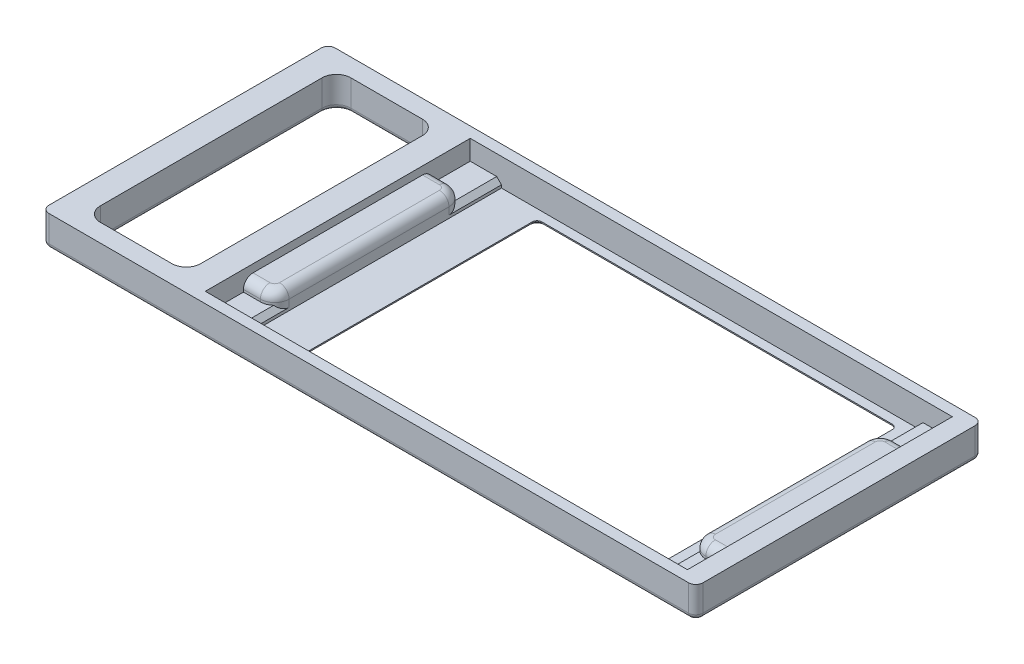
SolidWorks part; units mm, degrees
ref_plane "Front Plane" through (0, 0, 0) normal (0, 0, 1) x (1, 0, 0)
ref_plane "Top Plane" through (0, 0, 0) normal (0, 1, 0) x (1, 0, 0)
ref_plane "Right Plane" through (0, 0, 0) normal (1, 0, 0) x (0, 0, -1)
sketch "Sketch1" plane through (0, 0, 0) normal (0, 1, 0) x (1, 0, 0)
  line L1 (-68.5, 30) -> (68.5, 30)
  line L2 (-68.5, 30) -> (-68.5, -30)
  line L3 (-68.5, -30) -> (68.5, -30)
  line L4 (68.5, 30) -> (68.5, -30)
  line L5 (-68.5, 30) -> (68.5, -30) construction
  line L6 (-68.5, -30) -> (68.5, 30) construction
  point P0 (0, 0)
  dimension "D1" = 60
  dimension "D2" = 137
extrude "Boss-Extrude1" add sketch "Sketch1" along normal blind 6.5
sketch "Sketch2" plane through (0, 6.5, 0) normal (0, 1, 0) x (1, 0, 0)
  line L0 (0, 0) -> (47.9381, 0) construction
  line L1 (68.5, -30) -> (68.5, 30) construction
  line L2 (-36.5, 27.75) -> (64.5, 27.75)
  line L3 (-36.5, 27.75) -> (-36.5, -27.75)
  line L4 (-36.5, -27.75) -> (64.5, -27.75)
  line L5 (64.5, 27.75) -> (64.5, -27.75)
  line L6 (-36.5, 27.75) -> (64.5, -27.75) construction
  line L7 (-36.5, -27.75) -> (64.5, 27.75) construction
  point P3 (14, 0)
  dimension "D1" = 55.5
  dimension "D2" = 101
  dimension "D3" = 4
extrude "Cut-Extrude1" cut sketch "Sketch2" against normal blind 1.65
sketch "Sketch3" plane through (0, 4.85, 0) normal (0, 1, 0) x (1, 0, 0)
  line L0 (64.5, -27.75) -> (64.5, 27.75) construction
  line L1 (57.35, -27.75) -> (-29.95, -27.75)
  line L2 (57.35, -27.75) -> (57.35, 27.75)
  line L3 (57.35, 27.75) -> (-29.95, 27.75)
  line L4 (-29.95, -27.75) -> (-29.95, 27.75)
  line L5 (64.5, 27.75) -> (-36.5, 27.75) construction
  dimension "D1" = 7.15
  dimension "D2" = 87.3
  dimension "D3" = 55.5
  dimension "D4" = 0
extrude "Cut-Extrude2" cut sketch "Sketch3" against normal blind 4.1
sketch "Sketch4" plane through (0, 0.75, 0) normal (0, 1, 0) x (1, 0, 0)
  line L0 (0, 0) -> (36.8123, 0) construction
  line L1 (64.5, -27.75) -> (64.5, 27.75) construction
  line L2 (-20.6, 25.85) -> (54.8, 25.85)
  line L3 (-20.6, 25.85) -> (-20.6, -25.85)
  line L4 (-20.6, -25.85) -> (54.8, -25.85)
  line L5 (54.8, 25.85) -> (54.8, -25.85)
  line L6 (-20.6, 25.85) -> (54.8, -25.85) construction
  line L7 (-20.6, -25.85) -> (54.8, 25.85) construction
  point P3 (17.1, 0)
  dimension "D1" = 51.7
  dimension "D2" = 75.4
  dimension "D3" = 9.7
extrude "Cut-Extrude3" cut sketch "Sketch4" against normal through all
fillet "Fillet1" radius 1 4 edges at (54.8, 0.375, -25.85) (54.8, 0.375, 25.85) (-20.6, 0.375, 25.85) (-20.6, 0.375, -25.85)
sketch "Sketch6" plane through (0, 4.85, 0) normal (0, 1, 0) x (1, 0, 0)
  line L0 (57.35, -27.75) -> (57.35, 27.75) construction
  line L1 (64.5, -27.75) -> (57.35, -27.75)
  line L2 (64.5, -27.75) -> (64.5, -19.75)
  line L3 (64.5, -19.75) -> (57.35, -19.75)
  line L4 (57.35, -27.75) -> (57.35, -19.75)
  line L5 (57.35, -27.75) -> (57.35, 27.75) construction
  line L6 (64.5, 27.75) -> (57.35, 27.75)
  line L7 (64.5, 27.75) -> (64.5, 19.75)
  line L8 (64.5, 19.75) -> (57.35, 19.75)
  line L9 (57.35, 27.75) -> (57.35, 19.75)
  line L10 (-29.95, 27.75) -> (-29.95, -27.75) construction
  line L11 (-36.5, 27.75) -> (-29.95, 27.75)
  line L12 (-36.5, 27.75) -> (-36.5, 19.75)
  line L13 (-36.5, 19.75) -> (-29.95, 19.75)
  line L14 (-29.95, 27.75) -> (-29.95, 19.75)
  line L16 (-36.5, -27.75) -> (-29.95, -27.75)
  line L17 (-36.5, -27.75) -> (-36.5, -19.75)
  line L18 (-36.5, -19.75) -> (-29.95, -19.75)
  line L19 (-29.95, -27.75) -> (-29.95, -19.75)
  dimension "D1" = 8
  dimension "D2" = 8
  dimension "D3" = 8
  dimension "D4" = 8
extrude "Cut-Extrude4" cut sketch "Sketch6" against normal blind 2.5
fillet "Fillet2" radius 3 4 edges at (57.35, 3.6, -19.75) (57.35, 3.6, 19.75) (-29.95, 3.6, 19.75) (-29.95, 3.6, -19.75)
chamfer "Chamfer1" distance 0.5 angle 45 8 edges at (17.1, 0, -25.85) (-20.3071, 0, -25.5571) (54.5071, 0, -25.5571) (-20.6, 0, 0) (54.8, 0, 0) (-20.3071, 0, 25.5571) (54.5071, 0, 25.5571) (17.1, 0, 25.85)
sketch "Sketch7" plane through (0, 6.5, 0) normal (0, 1, 0) x (1, 0, 0)
  line L0 (0, 0) -> (-52.5, 0) construction
  line L1 (-36.5, 27.75) -> (-36.5, -27.75) construction
  line L2 (-63, 26.2268) -> (-42, 26.2268)
  line L3 (-63, 26.2268) -> (-63, -26.2268)
  line L4 (-63, -26.2268) -> (-42, -26.2268)
  line L5 (-42, 26.2268) -> (-42, -26.2268)
  line L6 (-63, 26.2268) -> (-42, -26.2268) construction
  line L7 (-63, -26.2268) -> (-42, 26.2268) construction
  line L8 (-68.5, 30) -> (-68.5, -30) construction
  dimension "D1" = 5.5
  dimension "D2" = 5.5
extrude "Cut-Extrude5" cut sketch "Sketch7" against normal through all
fillet "Fillet3" radius 3 4 edges at (-42, 3.25, 26.2268) (-63, 3.25, 26.2268) (-63, 3.25, -26.2268) (-42, 3.25, -26.2268)
fillet "Fillet5" radius 2 10 edges at (62.425, 4.85, 19.75) (58.2287, 4.85, 18.8713) (62.425, 4.85, -19.75) (58.2287, 4.85, -18.8713) (-34.725, 4.85, -19.75) (-30.8287, 4.85, -18.8713) (-34.725, 4.85, 19.75) (-30.8287, 4.85, 18.8713) (57.35, 4.85, 0) (-29.95, 4.85, 0)
chamfer "Chamfer3" distance 1 angle 45 4 edges at (57.35, 2.35, -22.25) (57.35, 2.35, 22.25) (-29.95, 2.35, 22.25) (-29.95, 2.35, -22.25)
fillet "Fillet6" radius 1.5 4 edges at (68.5, 3.25, 30) (-68.5, 3.25, 30) (-68.5, 3.25, -30) (68.5, 3.25, -30)
fillet "Fillet7" radius 1 16 edges at (-68.0607, 0, 29.5607) (-68.5, 0, 0) (-68.0607, 0, -29.5607) (0, 0, -30) (68.0607, 0, -29.5607) (68.5, 0, 0) (68.0607, 0, 29.5607) (-62.1213, 0, -25.3481) (-52.5, 0, -26.2268) (-42.8787, 0, -25.3481) (-42, 0, 0) (-42.8787, 0, 25.3481) (-52.5, 0, 26.2268) (-62.1213, 0, 25.3481) (0, 0, 30) (-63, 0, 0)
